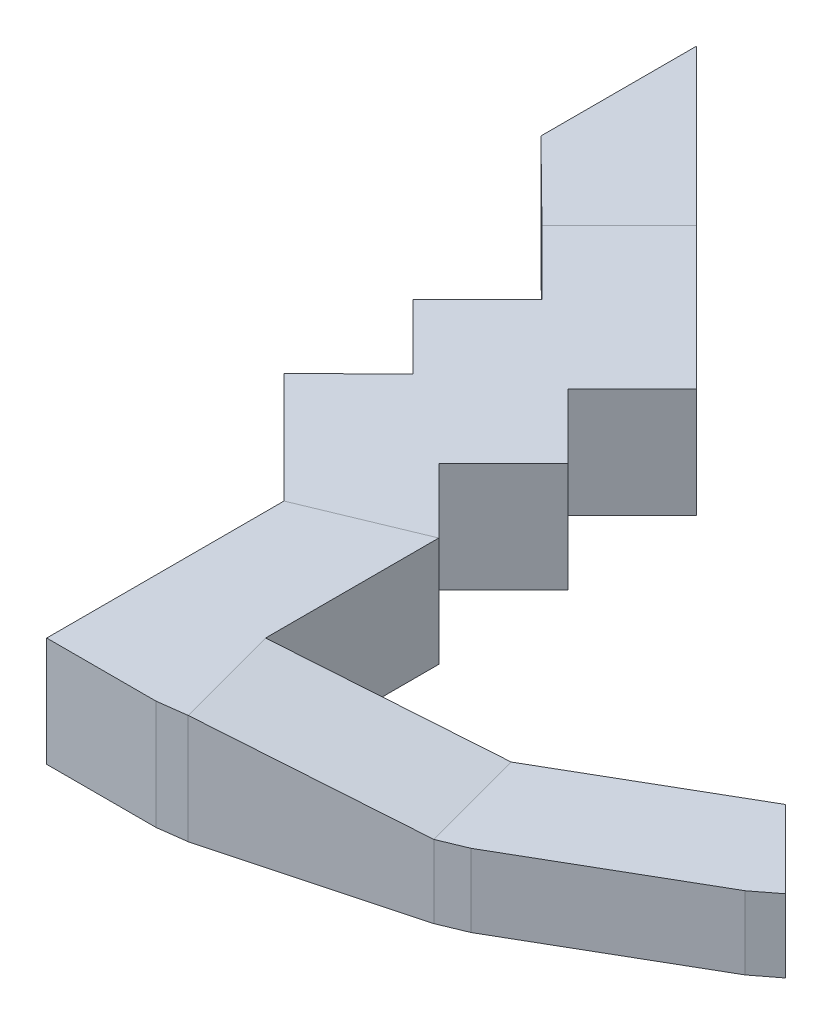
SolidWorks part; units mm, degrees
ref_plane "Front Plane" through (0, 0, 0) normal (0, 0, 1) x (1, 0, 0)
ref_plane "Top Plane" through (0, 0, 0) normal (0, 1, 0) x (1, 0, 0)
ref_plane "Right Plane" through (0, 0, 0) normal (1, 0, 0) x (0, 0, -1)
sketch "Sketch1" plane through (0, 0, 0) normal (0, 1, 0) x (1, 0, 0)
  line L0 (0, 0) -> (-1000, 0)
  line L1 (0, 0) -> (0, 600)
  line L2 (0, 600) -> (-1000, 600)
  line L3 (-1000, 0) -> (-2062.5184, -284.7009)
  line L4 (-2062.5184, -284.7009) -> (-3015.1464, -834.7009)
  line L5 (-1155.2914, 579.5555) -> (-2217.8098, 294.8545)
  line L6 (-1000, 600) -> (-1155.2914, 579.5555)
  line L7 (-3015.1464, -834.7009) -> (-3792.9638, -1612.5184)
  line L8 (-2217.8098, 294.8545) -> (-2362.5184, 234.9143)
  line L9 (-2362.5184, 234.9143) -> (-3315.1464, -315.0857)
  line L11 (-3439.4104, -410.4369) -> (-4217.2279, -1188.2543)
  line L12 (-3315.1464, -315.0857) -> (-3439.4104, -410.4369)
  line L26 (-8010.1917, -2800.7727) -> (-7010.1917, -2800.7727)
  line L27 (-8010.1917, -2800.7727) -> (-8010.1917, -3400.7727)
  line L28 (-8010.1917, -3400.7727) -> (-7010.1917, -3400.7727)
  line L29 (-7010.1917, -2800.7727) -> (-5947.6733, -2516.0718)
  line L30 (-5947.6733, -2516.0718) -> (-4995.0453, -1966.0718)
  line L31 (-6854.9003, -3380.3282) -> (-5792.3819, -3095.6273)
  line L32 (-7010.1917, -3400.7727) -> (-6854.9003, -3380.3282)
  line L33 (-4995.0453, -1966.0718) -> (-4217.2279, -1188.2543)
  line L34 (-5792.3819, -3095.6273) -> (-5647.6733, -3035.687)
  line L35 (-5647.6733, -3035.687) -> (-4695.0453, -2485.687)
  line L36 (-4570.7813, -2390.3359) -> (-3792.9638, -1612.5184)
  line L37 (-4695.0453, -2485.687) -> (-4570.7813, -2390.3359)
extrude "Boss-Extrude1" add sketch "Sketch1" against normal blind 600
ref_plane "Plane1" through (-1000, 0, 0) normal (1, 0, 0) x (0, 0, -1)
sketch "Sketch7" plane through (0, 0, 0) normal (0, 0, 1) x (1, 0, 0)
  line L0 (-3015.1464, -400) -> (-3015.1464, 0)
  line L1 (-2062.5184, -600) -> (-2062.5184, 0) construction
  line L2 (-3015.1464, -400) -> (-2062.5184, -400)
  line L3 (-3015.1464, -600) -> (-3015.1464, 0) construction
  line L4 (-1000, -600) -> (-1000, 0)
  line L5 (-2062.5184, -400) -> (-1000, -600)
extrude "Cut-Extrude9" cut sketch "Sketch7" against normal through all and the other way through all
sketch "Sketch8" plane through (0, 0, 0) normal (0, 0, 1) x (1, 0, 0)
  line L0 (-1000, -600) -> (0, -600)
  line L1 (0, -600) -> (0, 0)
  line L2 (-1000, -600) -> (-1000, 0)
  line L5 (-4570.7813, -600) -> (-4570.7813, 0) construction
  line L6 (-4570.7813, -200) -> (-3015.1464, -400)
  line L7 (-4570.7813, -200) -> (-4695.0453, -200)
  line L8 (-4695.0453, -600) -> (-4695.0453, 0) construction
  line L9 (-4695.0453, -200) -> (-4695.0453, 0)
extrude "Cut-Extrude-Thin1" cut sketch "Sketch8" against normal through all thin thin type one direction wall 10
sketch "Sketch9" plane through (-1090.2227, 0, -1090.2227) normal (0.7071, 0, 0.7071) x (0.7071, 0, -0.7071)
  line L0 (-4922.2531, 0) -> (-4922.2531, -200)
  line L1 (-4922.2531, -600) -> (-4922.2531, 0) construction
  line L3 (-2722.2531, -400) -> (-2722.2531, 0)
  line L4 (-2722.2531, -400) -> (-2722.2531, 0) construction
sketch "Sketch14" plane through (0, -400, 0) normal (0, 1, 0) x (1, 0, 0)
  line L0 (-3015.1464, -834.7009) -> (-3439.4104, -410.4369)
  line L1 (-3015.1464, -834.7009) -> (-3015.1464, -141.8806)
  line L2 (-3015.1464, -834.7009) -> (-3015.1464, -141.8806) construction
  line L3 (-3015.1464, -834.7009) -> (-3015.1464, -141.8806) construction
  line L4 (-3315.1464, -315.0857) -> (-3015.1464, -141.8806)
  line L5 (-3439.4104, -410.4369) -> (-3315.1464, -315.0857)
extrude "Cut-Extrude40" cut sketch "Sketch14" along normal blind 400
sketch "Sketch17" plane through (-1090.2227, 0, -1090.2227) normal (0.7071, 0, 0.7071) x (0.7071, 0, -0.7071)
  line L0 (-2722.2531, -400) -> (-2722.2531, 0)
  line L1 (-4922.2531, -600) -> (-4922.2531, 0) construction
  line L2 (-2722.2531, -400) -> (-4922.2531, -200)
  line L3 (-4922.2531, -200) -> (-4922.2531, 0)
extrude "Cut-Extrude42" cut sketch "Sketch17" along normal through all and the other way through all flip side to cut
sketch "Sketch18" plane through (0, 0, 0) normal (0, 1, 0) x (1, 0, 0)
  line L0 (-4570.7813, -2390.3359) -> (-4995.0453, -1966.0718)
  line L1 (-4995.0453, -1966.0718) -> (-5947.6733, -2516.0718)
  line L2 (-5947.6733, -2516.0718) -> (-5792.3819, -3095.6273)
  line L3 (-5792.3819, -3095.6273) -> (-5647.6733, -3035.687) construction
  line L4 (-6854.9003, -3380.3282) -> (-5792.3819, -3095.6273) construction
  line L5 (-5792.3819, -3095.6273) -> (-5647.6733, -3035.687)
  line L6 (-5647.6733, -3035.687) -> (-4695.0453, -2485.687)
  line L7 (-4695.0453, -2485.687) -> (-4570.7813, -2390.3359)
extrude "Cut-Extrude43" cut sketch "Sketch18" against normal blind 200
sketch "Sketch19" plane through (385.8908, 0, 1440.1641) normal (0.2588, 0, 0.9659) x (0.9659, 0, -0.2588)
  line L0 (-6396.2185, -200) -> (-7496.2185, 0)
  line L1 (-6396.2185, -200) -> (-6396.2185, 0)
extrude "Cut-Extrude44" cut sketch "Sketch19" against normal through all and the other way through all
sketch "Sketch20" plane through (0, 0, 0) normal (0, 1, 0) x (1, 0, 0)
  line L0 (-7010.1917, -3400.7727) -> (-7010.1917, -2800.7727)
  line L1 (-7010.1917, -2800.7727) -> (-8010.1917, -2800.7727)
  line L2 (-7010.1917, -2800.7727) -> (-8010.1917, -2800.7727) construction
  line L3 (-8010.1917, -2800.7727) -> (-8010.1917, -3400.7727)
  line L4 (-8010.1917, -3400.7727) -> (-7010.1917, -3400.7727)
extrude "Cut-Extrude45" cut sketch "Sketch20" against normal blind 600
sketch "Sketch21" plane through (0, 0, 0) normal (0, 1, 0) x (1, 0, 0)
  line L0 (0, 0) -> (-10, 600)
  line L1 (-10, 600) -> (-990, 600)
  line L2 (-990, 600) -> (-1000, 0)
  line L4 (-1000, 0) -> (0, 0)
extrude "Cut-Extrude46" cut sketch "Sketch21" against normal blind 600
sketch "Sketch22" plane through (0, 0, 0) normal (0, 1, 0) x (1, 0, 0)
  line L0 (-7010.1917, -3400.7727) -> (-7610.1917, -3400.7727)
  line L1 (-7010.1917, -3400.7727) -> (-7010.1917, -2800.7727)
  line L2 (-7010.1917, -2800.7727) -> (-7010.1917, -1850.7727)
  line L3 (-7610.1917, -3400.7727) -> (-7610.1917, -2099.7727)
  line L4 (-7610.1917, -2099.7727) -> (-7010.1917, -1850.7727)
extrude "Boss-Extrude2" add sketch "Sketch22" against normal blind 600
sketch "Sketch23" plane through (0, 0, 0) normal (0, 1, 0) x (1, 0, 0)
  line L0 (-7010.1917, -1850.7727) -> (-7363.7451, -1497.2194)
  line L3 (-7610.1917, -2099.7727) -> (-8216.4721, -1493.4923)
  line L4 (-8216.4721, -1493.4923) -> (-7858.7198, -1143.666)
  line L5 (-7858.7198, -1143.666) -> (-8212.2732, -790.1126)
  line L6 (-7363.7451, -1497.2194) -> (-7010.1917, -1143.666)
  line L7 (-7010.1917, -1143.666) -> (-7363.7451, -790.1126)
  line L10 (-7858.7198, -436.5592) -> (-8212.2732, -790.1126)
  line L11 (-7858.7198, -436.5592) -> (-8212.2732, -83.0058)
  line L12 (-7363.7451, -790.1126) -> (-7010.1917, -436.5592)
  line L13 (-7010.1917, -436.5592) -> (-7369.5272, -77.2237)
  line L14 (-7369.5272, -77.2237) -> (-7793.7913, 347.0404)
  line L15 (-7858.7198, 270.5476) -> (-7793.7913, 347.0404)
  line L16 (-8212.2732, -83.0058) -> (-7858.7198, 270.5476)
  line L17 (-7610.1917, -2099.7727) -> (-7010.1917, -1850.7727)
extrude "Boss-Extrude3" add sketch "Sketch23" against normal blind 600
sketch "Sketch24" plane through (0, 0, 0) normal (0, 1, 0) x (1, 0, 0)
  line L0 (-7793.7913, 347.0404) -> (-8639.4431, 1192.6922)
  line L1 (-8212.2732, -83.0058) -> (-8639.4431, 338.3624)
  line L2 (-8639.4431, 338.3624) -> (-8639.4431, 1192.6922)
  line L3 (-8212.2732, -83.0058) -> (-7793.7913, 347.0404)
  line L4 (-8212.2732, -83.0058) -> (-7793.7913, 347.0404)
  dimension "D1" = 45
extrude "Boss-Extrude4" add sketch "Sketch24" against normal blind 600 separate body contours L1 L3 L0 L2
sketch "Sketch27" plane through (-4176.5499, 0, -4064.2397) normal (0.7167, 0, 0.6974) x (0.6974, 0, -0.7167)
  line L1 (-5786.77, 0) -> (-5186.7143, 0)
  line L2 (-5786.77, 0) -> (-5786.77, -600)
  line L3 (-5786.77, -600) -> (-5186.7143, -600)
  line L4 (-5186.7143, 0) -> (-5186.7143, -600)
extrude "Boss-Extrude5" add sketch "Sketch27" along normal up to next
sketch "Sketch29" plane through (0, 0, 0) normal (0, 1, 0) x (1, 0, 0)
  line L0 (-7610.1917, -2099.7727) -> (-7010.1917, -1850.7727)
  line L1 (-8212.2732, -83.0058) -> (-7788.0092, 341.2583)
  line L2 (-7010.1917, -436.5592) -> (-8639.4431, 1192.6922) construction
  line L3 (-8212.2732, -83.0058) -> (-7858.7198, -436.5592)
  line L4 (-7858.7198, -436.5592) -> (-8212.2732, -790.1126)
  line L5 (-8212.2732, -790.1126) -> (-7858.7198, -1143.666)
  line L6 (-7858.7198, -1143.666) -> (-8216.4721, -1493.4923)
  line L7 (-8216.4721, -1493.4923) -> (-7610.1917, -2099.7727)
  line L8 (-7010.1917, -1850.7727) -> (-7363.7451, -1497.2194)
  line L9 (-7363.7451, -1497.2194) -> (-7010.1917, -1143.666)
  line L10 (-7010.1917, -1143.666) -> (-7363.7451, -790.1126)
  line L11 (-7363.7451, -790.1126) -> (-7010.1917, -436.5592)
  line L12 (-7363.7451, -790.1126) -> (-7010.1917, -436.5592) construction
  line L13 (-7010.1917, -436.5592) -> (-7788.0092, 341.2583)
split line "Split Line1"
sketch "Sketch30" plane through (-3723.3754, 0, 3723.3754) normal (0.7071, 0, -0.7071) x (-0.7071, 0, -0.7071)
  line L0 (5748.2601, 0) -> (5748.2601, -600)
  line L1 (4648.2601, -600) -> (6952.3696, -600) construction
split line "Split Line2"
sketch "Sketch31" plane through (-222.2787, 0, -829.5555) normal (-0.2588, 0, -0.9659) x (-0.9659, 0, 0.2588)
  line L0 (1905.1563, -400) -> (1905.1563, -600)
  line L1 (965.9258, -600) -> (2065.9258, -600) construction
split line "Split Line3"
sketch "Sketch32" plane through (-143.2934, -761.2596, 0) normal (0.185, 0.9827, 0) x (0.9827, -0.185, 0)
  line L2 (-1952.9293, 25.8819) -> (-950.7608, 289.7777)
  line L3 (-1952.9293, -284.7009) -> (-1952.9293, 336.4648) construction
  line L4 (-950.7608, 289.7777) -> (-871.7516, 300)
  line L5 (-871.7516, 0) -> (-871.7516, 600) construction
sketch "Sketch33" plane through (0, -400, 0) normal (0, 1, 0) x (1, 0, 0)
  line L2 (-3165.1464, -574.8933) -> (-2140.1641, 5.0768)
  line L3 (-2140.1641, 5.0768) -> (-2062.5184, 25.8819)
  line L4 (-3165.1464, -574.8933) -> (-3227.2784, -622.5689)
  line L5 (-3439.4104, -410.4369) -> (-3015.1464, -834.7009) construction
sketch "Sketch34" plane through (-41.2803, -642.1704, 41.2803) normal (0.064, 0.9959, -0.064) x (0.9979, -0.0639, 0.0041)
  line L0 (-4751.3795, -2160.8873) -> (-3192.5469, -595.6266)
  line L1 (-4963.9475, -1949.1922) -> (-4538.8114, -2372.5824) construction
sketch "Sketch35" plane through (0, -200, 0) normal (0, 1, 0) x (1, 0, 0)
  line L3 (-5788.2678, -2770.4492) -> (-4845.0453, -2225.8794)
  line L4 (-4845.0453, -2225.8794) -> (-4782.9133, -2178.2038)
  line L5 (-5788.2678, -2770.4492) -> (-5870.0276, -2805.8495)
  line L6 (-5947.6733, -2516.0718) -> (-5792.3819, -3095.6273) construction
sketch "Sketch36" plane through (-231.7053, -1319.3345, 62.0853) normal (0.1728, 0.9839, -0.0463) x (0.985, -0.1726, 0.0081)
  line L0 (-5724.4252, -2793.3468) -> (-6803.1693, -3087.1342)
  line L1 (-6724.3379, -3376.5917) -> (-6882.0008, -2797.6768) construction
sketch "Sketch37" plane through (0, 0, 0) normal (0, 1, 0) x (1, 0, 0)
  line L0 (-7010.1917, -3400.7727) -> (-7010.1917, -2800.7727)
  line L1 (-7010.1917, -3100.7727) -> (-7310.1917, -3100.7727)
  line L2 (-7010.1917, -3100.7727) -> (-6932.546, -3090.5505)
  line L3 (-7310.1917, -3100.7727) -> (-7310.1917, -1975.2727)
  line L4 (-7010.1917, -1850.7727) -> (-7610.1917, -2099.7727) construction
  line L5 (-7823.3645, -754.7572) -> (-7681.9431, -613.3359)
  line L12 (-7858.7198, -436.5592) -> (-8212.2732, -790.1126) construction
  line L14 (-8212.2732, -790.1126) -> (-7858.7198, -1143.666) construction
  line L16 (-8212.2732, -83.0058) -> (-7788.0092, 341.2583) construction
  line L22 (-7310.1917, -1975.2727) -> (-7752.7718, -1532.6927)
  line L36 (-7752.7718, -1532.6927) -> (-7399.1004, -1179.0213)
  line L40 (-7575.8771, -1002.2446) -> (-7399.1004, -1179.0213)
  line L42 (-7575.8771, -1002.2446) -> (-7646.5878, -931.5339)
  line L43 (-7646.5878, -931.5339) -> (-7823.3645, -754.7572)
  line L44 (-7681.9431, -613.3359) -> (-7469.8111, -401.2038)
  line L45 (-7469.8111, -401.2038) -> (-8000.1412, 129.1262)
sketch "Sketch38" plane through (0, -600, 0) normal (0, -1, 0) x (1, 0, 0)
  line L0 (-4570.7813, 2390.3359) -> (-4995.0453, 1966.0718)
  line L1 (-4995.0453, 1966.0718) -> (-3439.4104, 410.4369)
  line L2 (-3439.4104, 410.4369) -> (-3315.1464, 315.0857)
  line L3 (-3315.1464, 315.0857) -> (-2217.8098, -294.8545)
  line L4 (-2217.8098, -294.8545) -> (-2062.5184, -336.4648)
  line L5 (-2062.5184, -336.4648) -> (-1000, -600)
  line L6 (-1000, -600) -> (-1000, 0)
  line L7 (-1000, 0) -> (-2062.5184, 284.7009)
  line L8 (-2062.5184, 284.7009) -> (-3015.1464, 834.7009)
  line L9 (-3015.1464, 834.7009) -> (-4570.7813, 2390.3359)
extrude "Cut-Extrude47" cut sketch "Sketch38" against normal blind 500
sketch "Sketch39" plane through (0, -600, 0) normal (0, -1, 0) x (-1, 0, 0)
  line L0 (1155.2914, 579.5555) -> (1000, 600)
  line L1 (1000, 600) -> (2062.5184, 336.4648)
  line L2 (2062.5184, 336.4648) -> (1155.2914, 579.5555)
extrude "Cut-Extrude48" cut sketch "Sketch39" against normal blind 500
sketch "Sketch40" plane through (0, -600, 0) normal (0, -1, 0) x (-1, 0, 0)
  line L0 (2362.5184, 234.9143) -> (2217.8098, 294.8545)
  line L1 (2217.8098, 294.8545) -> (3315.1464, -315.0857)
  line L2 (3315.1464, -315.0857) -> (2362.5184, 234.9143)
  line L3 (2362.5184, 234.9143) -> (2362.5645, 234.2169)
extrude "Cut-Extrude49" cut sketch "Sketch40" against normal blind 500
